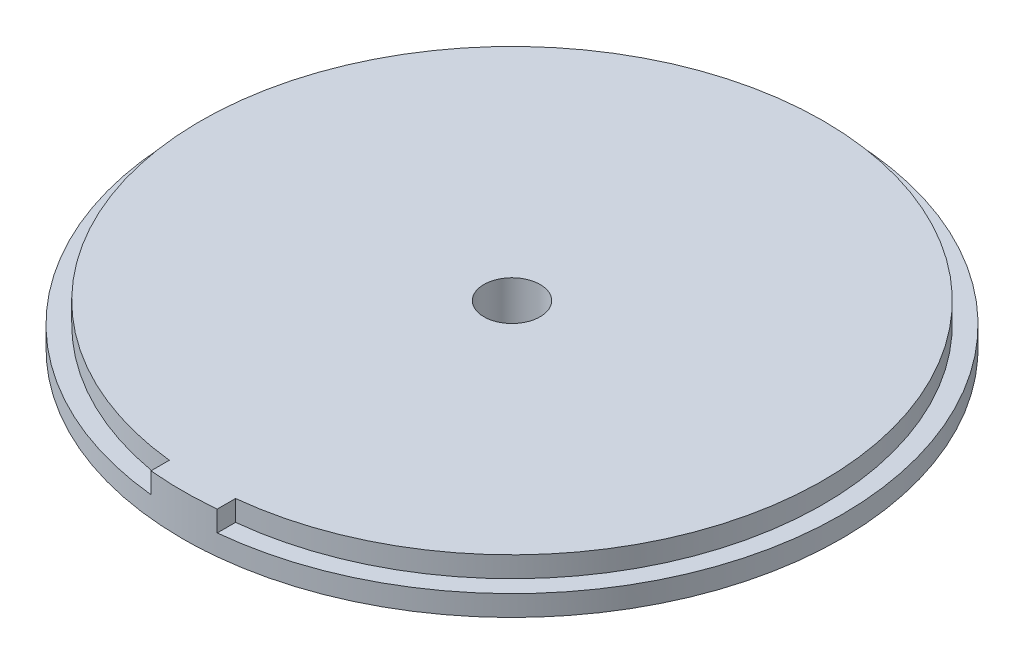
SolidWorks part; units mm, degrees
ref_plane "Front Plane" through (0, 0, 0) normal (0, 0, 1) x (1, 0, 0)
ref_plane "Top Plane" through (0, 0, 0) normal (0, 1, 0) x (1, 0, 0)
ref_plane "Right Plane" through (0, 0, 0) normal (1, 0, 0) x (0, 0, -1)
sketch "Sketch1" plane through (0, 0, 0) normal (0, 1, 0) x (1, 0, 0)
  circle A0 centre (0, 0) radius 25.273
  dimension "D1" = 50.546
extrude "Boss-Extrude1" add sketch "Sketch1" along normal blind 1.5875
sketch "Sketch2" plane through (0, 1.5875, 0) normal (0, 1, 0) x (1, 0, 0)
  circle A0 centre (0, 0) radius 23.876
  dimension "D1" = 47.752
extrude "Boss-Extrude2" add sketch "Sketch2" along normal blind 1.5875
sketch "Sketch3" plane through (0, 1.5875, 0) normal (0, 1, 0) x (1, 0, 0)
  line L0 (-2.54, -25.145) -> (-2.54, -23.7405)
  line L1 (2.54, -25.145) -> (2.54, -23.7405)
  circle A0 centre (0, 0) radius 25.273 construction
  circle A1 centre (0, 0) radius 23.876 construction
  circle A2 centre (0, 0) radius 23.876 construction
  arc A3 (-2.54, -23.7405) -> (2.54, -23.7405) centre (0, 0) ccw
  arc A4 (-2.54, -25.145) -> (2.54, -25.145) centre (0, 0) ccw
  dimension "D1" = 2.54
  dimension "D2" = 2.54
extrude "Boss-Extrude3" add sketch "Sketch3" along normal up to surface (1.5875 mm away) up to face at (0, 3.175, 23.876)
sketch "Sketch5" plane through (0, 3.175, 0) normal (0, 1, 0) x (1, 0, 0)
  point P0 (0, 0)
hole_wizard "#8 Clearance Hole1" positions "3DSketch1" profile "Sketch6" hole size "#8" standard "ANSI Inch" end condition up to next
sketch3d "3DSketch1"
  point P0 (0, 3.175, 0)
sketch "Sketch6" plane through (0, 3.175, 0) normal (1, 0, 0) x (0, 0, 1)
  line L0 (0, 0) -> (0, 3.175)
  line L1 (0, 3.175) -> (2.1526, 3.175)
  line L2 (2.1526, 3.175) -> (2.1526, 0)
  line L5 (2.1526, 0) -> (0, 0)
  line L11 (0, -6.35) -> (0, 107.95) construction
  dimension "Thru Hole Dia." = 4.3053
  dimension "Thru Hole Depth" = 3.175
